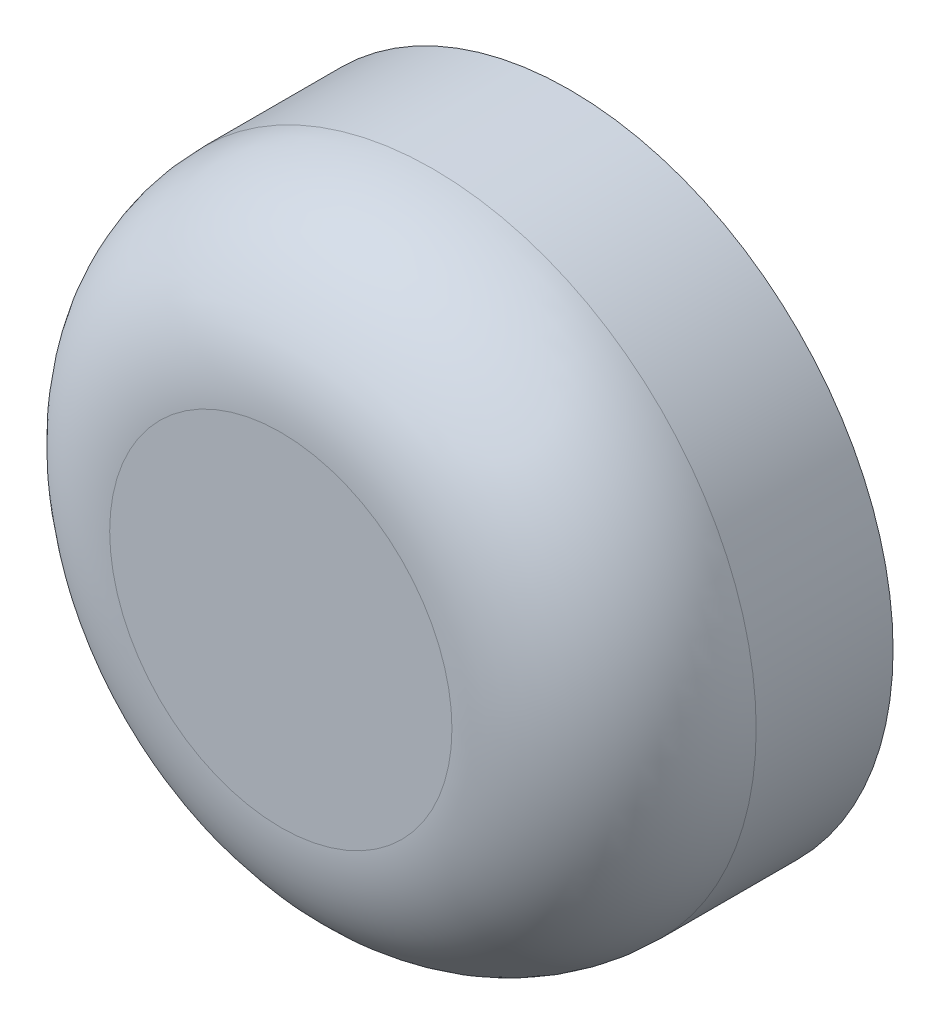
SolidWorks part; units mm, degrees
ref_plane "Piano frontale" through (0, 0, 0) normal (0, 0, 1) x (1, 0, 0)
ref_plane "Piano superiore" through (0, 0, 0) normal (0, 1, 0) x (1, 0, 0)
ref_plane "Piano destro" through (0, 0, 0) normal (1, 0, 0) x (0, 0, -1)
sketch "Schizzo1" plane through (0, 0, 0) normal (0, 0, 1) x (1, 0, 0)
  circle A0 centre (0, 0) radius 2.75
  circle A1 centre (0, 0) radius 4.25
  dimension "D1" = 5.5
  dimension "D2" = 1.5
extrude "Estrusione-Estrusione1" add sketch "Schizzo1" along normal blind 2.8
sketch "Schizzo2" plane through (0, 0, 2.8) normal (0, 0, 1) x (1, 0, 0)
  circle A0 centre (0, 0) radius 4.25
extrude "Estrusione-Estrusione2" add sketch "Schizzo2" along normal blind 1
fillet "Raccordo1" radius 2 1 edges at (4.25, 0, 3.8)
